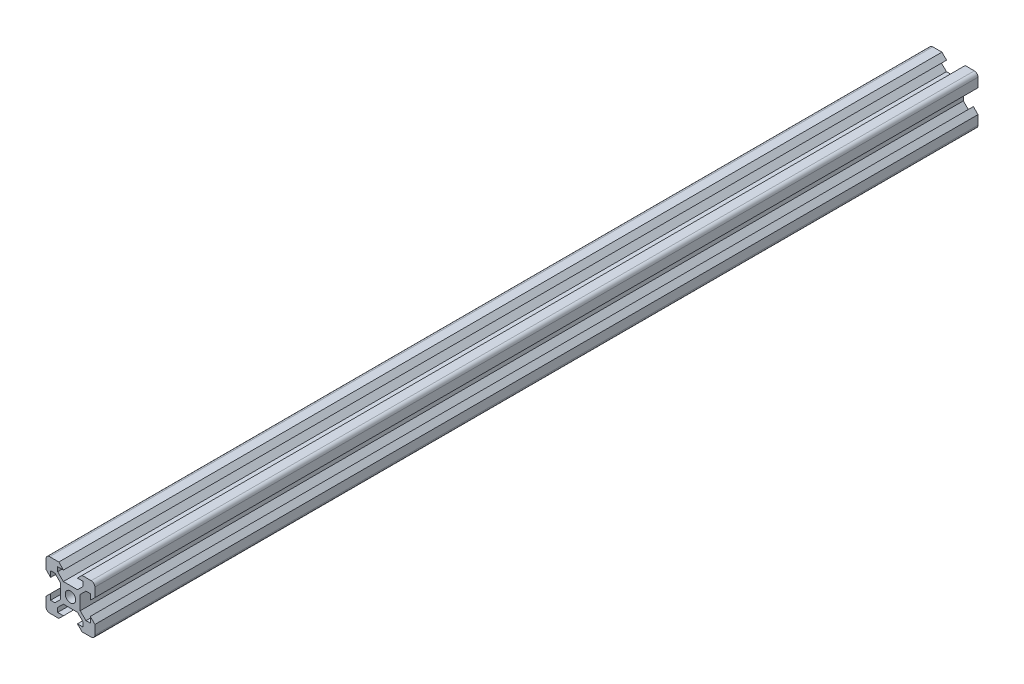
SolidWorks part; units mm, degrees
material "6061 Alloy"
ref_plane "Front Plane" through (0, 0, 0) normal (0, 0, 1) x (1, 0, 0)
ref_plane "Top Plane" through (0, 0, 0) normal (0, 1, 0) x (1, 0, 0)
ref_plane "Right Plane" through (0, 0, 0) normal (1, 0, 0) x (0, 0, -1)
sketch "Sketch1" plane through (0, 0, 0) normal (0, 0, 1) x (1, 0, 0)
  line L0 (15.6876, 55.3211) -> (115.0437, 55.3211) construction
  line L1 (8.1, 5.225) -> (8.1, 2.85)
  line L2 (-8.5, 10) -> (-4.75, 10)
  line L3 (-10, 8.5) -> (-10, 4.75)
  line L4 (-8.5, -10) -> (-4.75, -10)
  line L5 (10, 8.5) -> (10, 4.75)
  line L6 (6.325, 5.225) -> (4, 2.9)
  line L7 (-8.1, -2.85) -> (-8.1, -5.225)
  line L8 (-2.9, 4) -> (2.9, 4)
  line L9 (-4, 2.9) -> (-4, -2.9)
  line L10 (-2.9, -4) -> (2.9, -4)
  line L11 (4, 2.9) -> (4, -2.9)
  line L12 (2.85, -8.1) -> (5.225, -8.1)
  line L13 (-5.225, -8.1) -> (-2.85, -8.1)
  line L14 (5.225, 6.325) -> (2.9, 4)
  line L17 (-10, 4.75) -> (-8.1, 2.85)
  line L20 (4.75, -10) -> (8.5, -10)
  line L22 (-10, -4.75) -> (-10, -8.5)
  line L23 (10, -4.75) -> (10, -8.5)
  line L24 (-10, -4.75) -> (-8.1, -2.85)
  line L25 (-4.75, -10) -> (-2.85, -8.1)
  line L26 (4.75, -10) -> (2.85, -8.1)
  line L27 (10, -4.75) -> (8.1, -2.85)
  line L28 (10, 4.75) -> (8.1, 2.85)
  line L29 (-4.75, 10) -> (-2.85, 8.1)
  line L30 (4.75, 10) -> (2.85, 8.1)
  line L31 (8.1, -2.85) -> (8.1, -5.225)
  line L32 (6.325, -5.225) -> (8.1, -5.225)
  line L33 (5.225, -6.325) -> (5.225, -8.1)
  line L34 (4.75, 10) -> (8.5, 10)
  line L35 (2.85, 8.1) -> (5.225, 8.1)
  line L36 (10, -10) -> (10.975, -10.975) construction
  line L37 (-5.225, 8.1) -> (-2.85, 8.1)
  line L38 (-8.1, -5.225) -> (-6.325, -5.225)
  line L39 (-5.225, 6.325) -> (-2.9, 4)
  line L40 (-8.1, 5.225) -> (-8.1, 2.85)
  line L41 (-5.225, -6.325) -> (-5.225, -8.1)
  line L42 (-6.325, 5.225) -> (-4, 2.9)
  line L46 (-8.1, 5.225) -> (-6.325, 5.225)
  line L47 (-5.225, 8.1) -> (-5.225, 6.325)
  line L52 (8.1, 5.225) -> (6.325, 5.225)
  line L53 (5.225, 8.1) -> (5.225, 6.325)
  line L63 (4, -2.9) -> (6.325, -5.225)
  line L66 (2.9, -4) -> (5.225, -6.325)
  line L67 (-2.9, -4) -> (-5.225, -6.325)
  line L70 (-4, -2.9) -> (-6.325, -5.225)
  arc A0 (-8.5, -10) -> (-10, -8.5) centre (-8.5, -8.5) cw
  arc A1 (8.5, -10) -> (10, -8.5) centre (8.5, -8.5) ccw
  arc A2 (10, 8.5) -> (8.5, 10) centre (8.5, 8.5) ccw
  arc A3 (-8.5, 10) -> (-10, 8.5) centre (-8.5, 8.5) ccw
  circle A4 centre (0, 0) radius 2.125
  point P2 (0, 0)
  point P8 (0, 0)
  point P14 (-10, -10)
  point P20 (0, 0)
  point P49 (10, 10)
  point P52 (-10, 10)
  dimension "D3" = 1.5
  dimension "D4" = 4.25
  dimension "D1" = 20
  dimension "D2" = 20
  dimension "D13" = 5.25
  dimension "D14" = 5.25
  dimension "D15" = 90
  dimension "D16" = 5.25
  dimension "D17" = 5.25
  dimension "D18" = 5.25
  dimension "D19" = 5.25
  dimension "D20" = 5.25
  dimension "D21" = 5.25
  dimension "D22" = 90
  dimension "D23" = 90
  dimension "D24" = 90
  dimension "D25" = 2.85
  dimension "D26" = 2.85
  dimension "D27" = 2.85
  dimension "D28" = 2.85
extrude "Boss-Extrude1" add sketch "Sketch1" along normal blind 361.19
